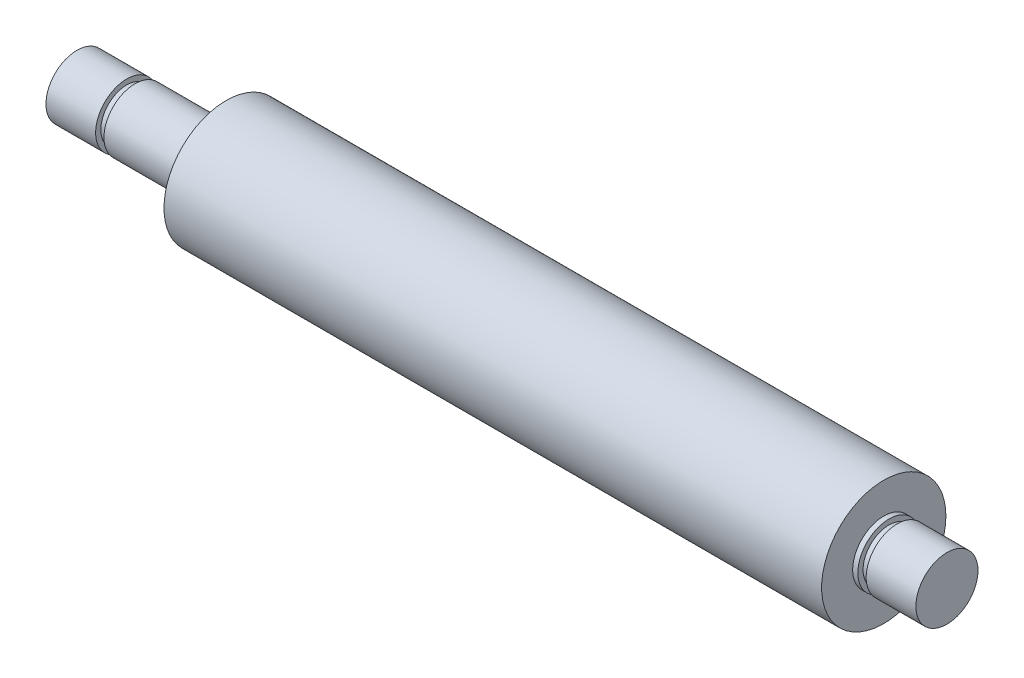
SolidWorks part; units mm, degrees
ref_plane "Front Plane" through (0, 0, 0) normal (0, 0, 1) x (1, 0, 0)
ref_plane "Top Plane" through (0, 0, 0) normal (0, 1, 0) x (1, 0, 0)
ref_plane "Right Plane" through (0, 0, 0) normal (1, 0, 0) x (0, 0, -1)
sketch "Sketch1" plane through (0, 0, 0) normal (0, 0, 1) x (1, 0, 0)
  line L0 (-42, 3) -> (-42, 0)
  line L1 (-42, 0) -> (42, 0)
  line L2 (42, 0) -> (42, 3)
  line L3 (42, 3) -> (37.2, 3)
  line L4 (37.2, 3) -> (37.2, 2.5)
  line L5 (37.2, 2.5) -> (36.4, 2.5)
  line L6 (36.4, 2.5) -> (36.4, 3)
  line L7 (36.4, 3) -> (35.9, 3)
  line L8 (35.9, 3) -> (35.9, 6)
  line L9 (35.9, 6) -> (-27.6, 6)
  line L10 (-27.6, 6) -> (-27.6, 3)
  line L11 (-27.6, 3) -> (-36.4, 3)
  line L12 (-36.4, 3) -> (-36.4, 2.5)
  line L13 (-36.4, 2.5) -> (-37.2, 2.5)
  line L14 (-37.2, 2.5) -> (-37.2, 3)
  line L15 (-37.2, 3) -> (-42, 3)
  line L16 (-42, 0) -> (42, 0) construction
revolve "Revolve1" add sketch "Sketch1" angle 360 about L16
